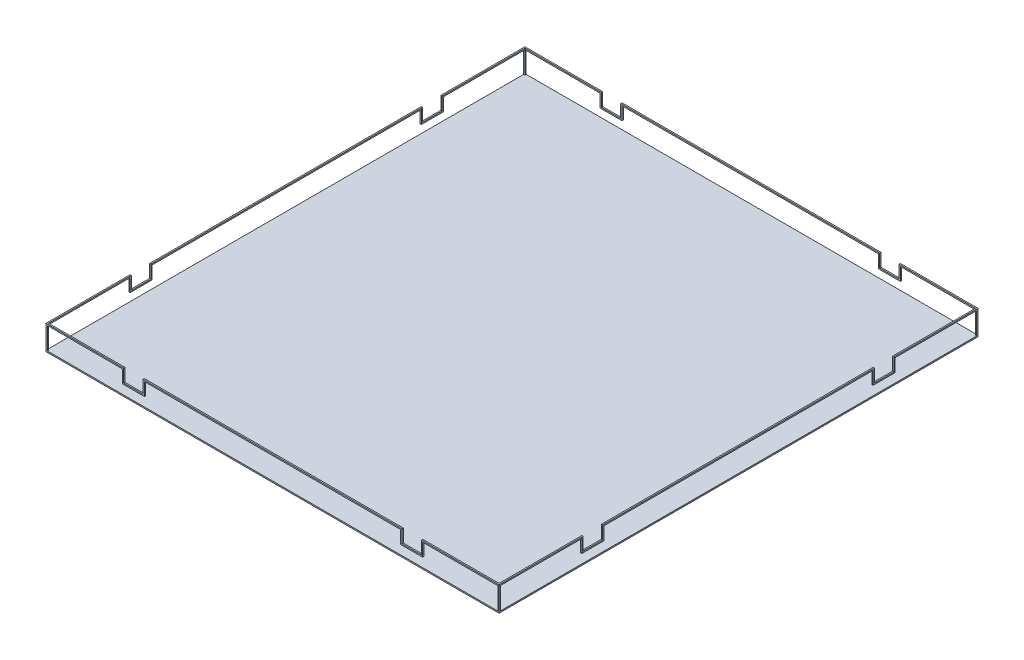
SolidWorks part; units mm, degrees
material "1060 合金"
ref_plane "前视基准面" through (0, 0, 0) normal (0, 0, 1) x (1, 0, 0)
ref_plane "上视基准面" through (0, 0, 0) normal (0, 1, 0) x (1, 0, 0)
ref_plane "右视基准面" through (0, 0, 0) normal (1, 0, 0) x (0, 0, -1)
sketch "草图1" plane through (0, 0, 0) normal (0, 1, 0) x (1, 0, 0)
  line L1 (0, 0) -> (35, 0)
  line L2 (0, 0) -> (0, 37)
  line L3 (0, 37) -> (35, 37)
  line L4 (35, 0) -> (35, 37)
  dimension "D1" = 35
  dimension "D2" = 37
sketch "草图2" plane through (0, 0, 0) normal (0, 0, 1) x (1, 0, 0)
  line L0 (0, 0) -> (0, 1.8)
  line L1 (0, 1.8) -> (6, 1.8)
  line L2 (6, 1.8) -> (6, 0.8)
  line L3 (6, 0.8) -> (7.5, 0.8)
  line L4 (7.5, 0.8) -> (7.5, 1.8)
  line L5 (7.5, 1.8) -> (27.5, 1.8)
  line L6 (35, 0) -> (35, 1.8)
  line L7 (27.5, 0.8) -> (27.5, 1.8)
  line L8 (29, 0.8) -> (27.5, 0.8)
  line L9 (29, 1.8) -> (29, 0.8)
  line L10 (35, 1.8) -> (29, 1.8)
  line L11 (0, 0) -> (35, 0) construction
  line L12 (17.5, 0) -> (17.5, -13.0154) construction
  point P10 (17.5, 1.8)
  dimension "D1" = 1.5
  dimension "D2" = 6
  dimension "D3" = 1.8
  dimension "D4" = 1
sketch "草图3" plane through (0, 0, 0) normal (1, 0, 0) x (0, 0, -1)
  line L0 (0, 0) -> (0, 1.8)
  line L1 (0, 1.8) -> (6.5, 1.8)
  line L2 (6.5, 1.8) -> (6.5, 0.8)
  line L3 (6.5, 0.8) -> (8, 0.8)
  line L4 (8, 0.8) -> (8, 1.8)
  line L5 (18.5, 0) -> (18.5, -7.2611) construction
  line L6 (0, 0) -> (37, 0) construction
  line L7 (8, 1.8) -> (29, 1.8)
  line L8 (37, 0) -> (37, 1.8)
  line L9 (29, 0.8) -> (29, 1.8)
  line L10 (30.5, 0.8) -> (29, 0.8)
  line L13 (30.5, 1.8) -> (30.5, 0.8)
  line L14 (37, 1.8) -> (30.5, 1.8)
  point P15 (18.5, 1.8)
  dimension "D1" = 1
  dimension "D2" = 1.8
  dimension "D3" = 6.5
  dimension "D4" = 1.5
extrude "凸台-拉伸1" add sketch "草图1" against normal blind 0.1
extrude "拉伸-薄壁2" add sketch "草图2" against normal blind 0.1 thin
extrude "拉伸-薄壁3" add sketch "草图3" along normal blind 0.1 thin
pattern_linear "阵列(线性)1" count 2 spacing 36.9 along (0, 0, -1) of "拉伸-薄壁2"
pattern_linear "阵列(线性)2" count 2 spacing 34.9 along (1, 0, 0) of "拉伸-薄壁3"
